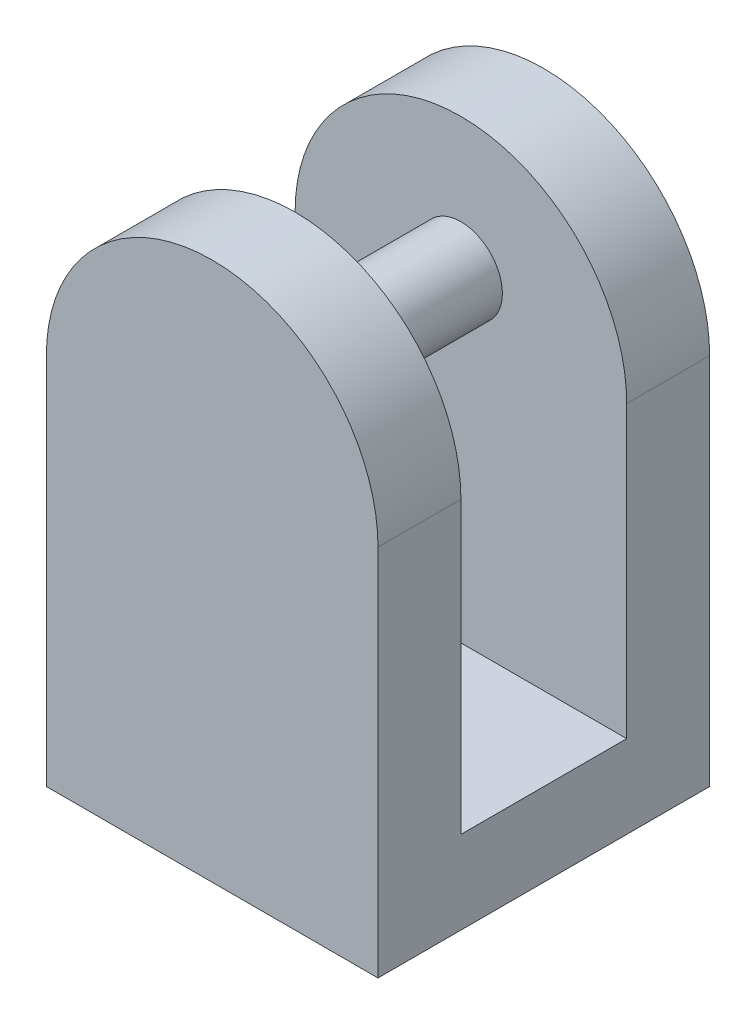
SolidWorks part; units mm, degrees
ref_plane "Front Plane" through (0, 0, 0) normal (0, 0, 1) x (1, 0, 0)
ref_plane "Top Plane" through (0, 0, 0) normal (0, 1, 0) x (1, 0, 0)
ref_plane "Right Plane" through (0, 0, 0) normal (1, 0, 0) x (0, 0, -1)
sketch "Sketch1" plane through (0, 0, 0) normal (0, 0, 1) x (1, 0, 0)
  line L0 (-10, 22.5) -> (-10, 0)
  line L5 (-10, 0) -> (10, 0)
  line L6 (10, 0) -> (10, 22.5)
  arc A0 (-10, 22.5) -> (10, 22.5) centre (0, 22.5) cw
  dimension "D1" = 20
  dimension "D2" = 10
  dimension "D4" = 22.5
extrude "Boss-Extrude1" add sketch "Sketch1" along normal mid plane 20
ref_plane "Plane1" through (0, 32.5, 0) normal (0, 1, 0) x (1, 0, 0)
sketch "Sketch3" plane through (0, 32.5, 0) normal (0, 1, 0) x (1, 0, 0)
  line L0 (10, -10) -> (10, 10) construction
  line L1 (-10, -5) -> (10, -5)
  line L2 (-10, -5) -> (-10, 5)
  line L3 (-10, 5) -> (10, 5)
  line L4 (10, -5) -> (10, 5)
  line L5 (-10, -5) -> (10, 5) construction
  line L6 (-10, 5) -> (10, -5) construction
  line L7 (10, 10) -> (-10, 10) construction
  point P0 (0, 0)
  dimension "D1" = 5
extrude "Cut-Extrude2" cut sketch "Sketch3" against normal blind 27.5
sketch "Sketch4" plane through (0, 0, 5) normal (0, 0, -1) x (-1, 0, 0)
  line L0 (10, 0) -> (-10, 0) construction
  circle A0 centre (0, 24.5) radius 2.5
  dimension "D1" = 5
  dimension "D2" = 24.5
extrude "Boss-Extrude2" add sketch "Sketch4" along normal up to surface (10 mm away) up to face at (0, 16.25, -5)
sketch "Sketch5" plane through (0, 5, 0) normal (0, 1, 0) x (1, 0, 0)
  circle A0 centre (0, 0) radius 1.25
  dimension "D1" = 2.5
extrude "Cut-Extrude4" cut sketch "Sketch5" against normal blind 10
sketch "Sketch6" plane through (0, 5, 0) normal (0, 1, 0) x (1, 0, 0)
  circle A0 centre (0, 0) radius 2.5
  dimension "D1" = 5
extrude "Cut-Extrude5" cut sketch "Sketch6" against normal blind 1.25
